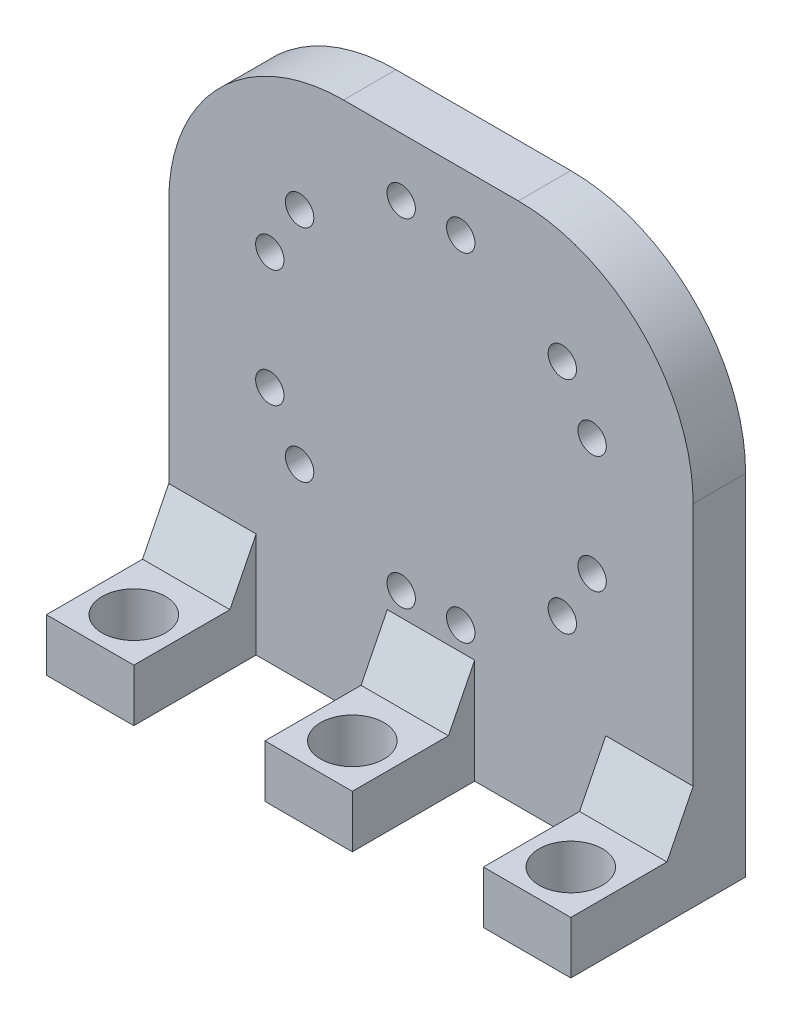
SolidWorks part; units mm, degrees
ref_plane "정면" through (0, 0, 0) normal (0, 0, 1) x (1, 0, 0)
ref_plane "윗면" through (0, 0, 0) normal (0, 1, 0) x (1, 0, 0)
ref_plane "우측면" through (0, 0, 0) normal (1, 0, 0) x (0, 0, -1)
sketch "Sketch1" plane through (0, 0, 0) normal (0, 0, 1) x (1, 0, 0)
  line L0 (30, 0) -> (0, 0) construction
  line L1 (-30, 30) -> (30, 30)
  line L2 (-30, 30) -> (-30, -30)
  line L3 (-30, -30) -> (30, -30)
  line L4 (30, 30) -> (30, -30)
  dimension "D1" = 60
  dimension "D2" = 60
  dimension "D3" = 30
extrude "Boss-Extrude1" add sketch "Sketch1" along normal blind 6
sketch "Sketch2" plane through (0, 0, 6) normal (0, 0, 1) x (1, 0, 0)
  line L0 (30, -30) -> (30, 30) construction
  line L1 (30, -24) -> (20, -24)
  line L2 (30, -24) -> (30, -30)
  line L3 (30, -30) -> (20, -30)
  line L4 (20, -24) -> (20, -30)
  line L5 (-30, -30) -> (30, -30) construction
  line L6 (0, 0) -> (0, -30) construction
  line L7 (0, -30) -> (25, -30) construction
  dimension "D1" = 25
  dimension "D2" = 10
  dimension "D3" = 6
extrude "Boss-Extrude2" add sketch "Sketch2" along normal blind 14 contours L1 L4 L3 L2
sketch "Sketch3" plane through (30, 0, 0) normal (1, 0, 0) x (0, 0, -1)
  line L0 (-6, -18) -> (-9, -24)
  line L1 (-6, -24) -> (-6, 30) construction
  line L2 (-20, -24) -> (-6, -24) construction
  line L3 (-9, -24) -> (-6, -24)
  line L4 (-6, -24) -> (-6, -18)
  dimension "D1" = 6
  dimension "D2" = 3
extrude "Boss-Extrude3" add sketch "Sketch3" against normal up to surface (10 mm away) up to face at (20, -27, 13)
sketch "Sketch4" plane through (0, -24, 0) normal (0, 1, 0) x (1, 0, 0)
  line L0 (25, -20) -> (25, 0) construction
  line L1 (30, -20) -> (20, -20) construction
  line L2 (30, 0) -> (-30, 0) construction
  circle A0 centre (25, -15) radius 3.625
  dimension "D1" = 7.25
  dimension "D2" = 5
extrude "Cut-Extrude1" cut sketch "Sketch4" against normal blind 15
pattern_linear "LPattern2" count 3 spacing 25 along (-1, 0, 0) of "Cut-Extrude1", "Boss-Extrude2", "Boss-Extrude3"
sketch "Sketch5" plane through (0, 0, 0) normal (0, 0, -1) x (-1, 0, 0)
  line L0 (0, 4) -> (0, 23.62) construction
  line L1 (0, 4) -> (3.407, 23.3219) construction
  line L2 (0, 4) -> (-3.407, 23.3219) construction
  line L3 (0, 4) -> (0, -30) construction
  line L4 (-5, -30) -> (5, -30) construction
  circle A0 centre (3.407, 23.3219) radius 1.625
  circle A1 centre (-3.407, 23.3219) radius 1.625
  dimension "D3" = 3.25
  dimension "D5" = 3.25
  dimension "D1" = 19.62
  dimension "D2" = 10
  dimension "D4" = 10
  dimension "D6" = 34
extrude "Cut-Extrude2" cut sketch "Sketch5" against normal blind 15
ref_plane "Plane1" through (0, 4, 0) normal (0, -1, 0) x (-1, 0, 0)
sketch "Sketch8" plane through (0, 4, 0) normal (0, -1, 0) x (-1, 0, 0)
  line L0 (0, 0) -> (0, -7.3713) construction
pattern_circular "CirPattern2" count 6 over 360 about axis through (0, 4, 0) along (0, 0, 1) of "Cut-Extrude2"
fillet "Fillet1" radius 20 2 edges at (-30, 30, 3) (30, 30, 3)
